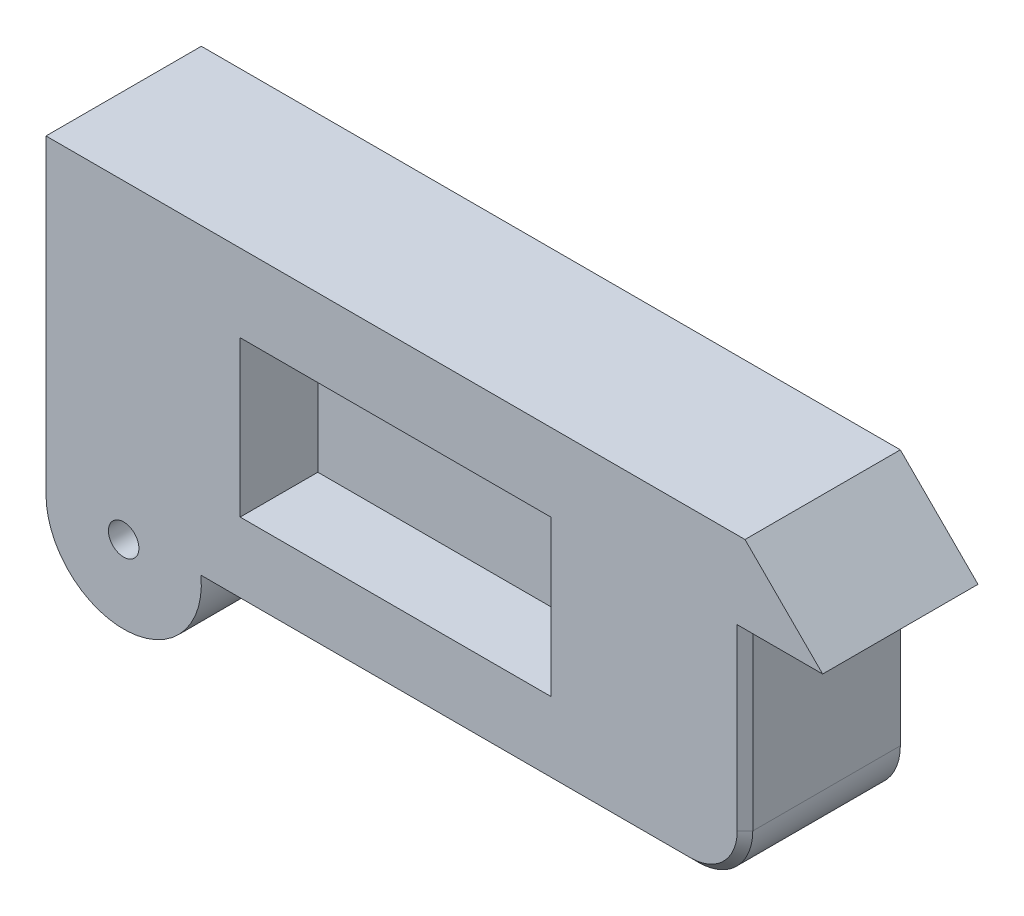
SolidWorks part; units mm, degrees
ref_plane "Front Plane" through (0, 0, 0) normal (0, 0, 1) x (1, 0, 0)
ref_plane "Top Plane" through (0, 0, 0) normal (0, 1, 0) x (1, 0, 0)
ref_plane "Right Plane" through (0, 0, 0) normal (1, 0, 0) x (0, 0, -1)
sketch "Sketch3" plane through (0, 0, 0) normal (0, 0, 1) x (1, 0, 0)
  line L0 (2286, 762) -> (2540, 762)
  line L1 (508, 0) -> (2286, 0)
  line L2 (0, 0) -> (0, 1016)
  line L3 (0, 1016) -> (2286, 1016)
  line L4 (2286, 0) -> (2286, 762)
  line L5 (2540, 762) -> (2286, 1016)
  line L6 (2540, 762) -> (2955.9892, 762) construction
  arc A0 (0, 0) -> (508, 0) centre (254, 0) ccw
  point P8 (508, 0)
  dimension "D7" = 254
  dimension "D1" = 2286
  dimension "D2" = 1016
  dimension "D3" = 762
  dimension "D4" = 254
  dimension "D5" = 135
  dimension "D6" = 1778
extrude "Boss-Extrude1" add sketch "Sketch3" along normal blind 508
sketch "Sketch6" plane through (0, 0, 508) normal (0, 0, 1) x (1, 0, 0)
  point P0 (254, 0)
  point P1 (0, 0)
hole_wizard "Tap Drill for 4-12 Tap1" positions "3DSketch4" profile "Sketch7" hole size "4-12" standard "Superior" end condition through all
sketch3d "3DSketch4"
  point P0 (254, 0, 508)
sketch "Sketch7" plane through (254, 0, 508) normal (1, 0, 0) x (0, -1, 0)
  line L0 (0, 0) -> (0, 508)
  line L1 (0, 508) -> (49.8284, 508)
  line L2 (49.8284, 508) -> (49.8284, 0)
  line L5 (49.8284, 0) -> (0, 0)
  line L11 (0, -6.35) -> (0, 107.95) construction
  dimension "Thru Hole Dia." = 99.6569
  dimension "Thru Hole Depth" = 508
sketch "Sketch8" plane through (0, 0, 508) normal (0, 0, 1) x (1, 0, 0)
  line L0 (2286, 0) -> (2286, 762) construction
  line L1 (635, 254) -> (1651, 254)
  line L2 (635, 254) -> (635, 762)
  line L3 (635, 762) -> (1651, 762)
  line L4 (1651, 254) -> (1651, 762)
  line L5 (2286, 1016) -> (0, 1016) construction
  point P4 (1784.7346, 794.626)
  dimension "D1" = 1016
  dimension "D2" = 508
  dimension "D3" = 635
  dimension "D4" = 254
extrude "Cut-Extrude1" cut sketch "Sketch8" against normal blind 254
fillet "Fillet1" radius 177.8 1 edges at (2286, 0, 254)
chamfer "Chamfer1" distance 25.4 angle 45 3 edges at (2286, 469.9, 508) (2233.9236, 52.0764, 508) (1308.1, 0, 508)
